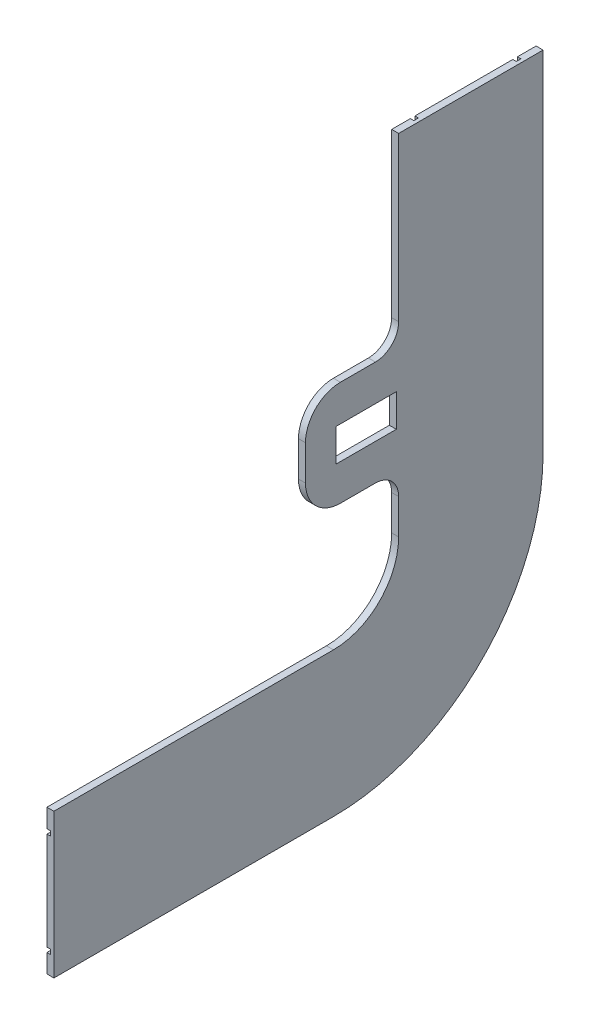
SolidWorks part; units mm, degrees
ref_plane "Front Plane" through (0, 0, 0) normal (0, 0, 1) x (1, 0, 0)
ref_plane "Top Plane" through (0, 0, 0) normal (0, 1, 0) x (1, 0, 0)
ref_plane "Right Plane" through (0, 0, 0) normal (1, 0, 0) x (0, 0, -1)
sketch "Sketch1" plane through (0, 0, 0) normal (1, 0, 0) x (0, 0, -1)
  line L0 (90, 0) -> (0, 0) construction
  line L1 (0, 0) -> (0, -90) construction
  line L2 (0, -28) -> (-120, -28)
  line L3 (-120, -28) -> (-120, -90)
  line L4 (-120, -90) -> (0, -90)
  line L5 (28, 0) -> (28, 150)
  line L6 (28, 150) -> (90, 150)
  line L7 (90, 150) -> (90, 0)
  arc A0 (0, -90) -> (90, 0) centre (0, 0) ccw
  arc A1 (0, -28) -> (28, 0) centre (0, 0) ccw
  dimension "D1" = 180
  dimension "D2" = 62
  dimension "D3" = 120
  dimension "D4" = 150
extrude "Boss-Extrude1" add sketch "Sketch1" along normal blind 3
sketch "Sketch2" plane through (3, 0, 0) normal (1, 0, 0) x (0, 0, -1)
  line L0 (0, 0) -> (90, 0) construction
  line L1 (0, 0) -> (0, -90) construction
  line L2 (0, -38) -> (-120, -38)
  line L3 (-120, -28) -> (-120, -90) construction
  line L4 (0, -80) -> (-120, -80)
  line L5 (38, 0) -> (38, 150)
  line L6 (90, 150) -> (28, 150) construction
  line L7 (80, 0) -> (80, 150)
  line L8 (36, 0) -> (36, 150)
  line L9 (0, -36) -> (-120, -36)
  line L10 (0, -82) -> (-120, -82)
  line L11 (82, 0) -> (82, 150)
  line L12 (36, 150) -> (38, 150)
  line L13 (80, 150) -> (82, 150)
  line L14 (-120, -80) -> (-120, -82)
  line L15 (-120, -36) -> (-120, -38)
  arc A0 (0, -38) -> (38, 0) centre (0, 0) ccw
  arc A1 (0, -80) -> (80, 0) centre (0, 0) ccw
  arc A2 (0, -36) -> (36, 0) centre (0, 0) ccw
  arc A3 (0, -82) -> (82, 0) centre (0, 0) ccw
  dimension "D1" = 42
  dimension "D2" = 80
  dimension "D3" = 2
  dimension "D4" = 2
extrude "Cut-Extrude1" cut sketch "Sketch2" against normal blind 1.5
mirror "Mirror1" about plane through (3, 0, 0) normal (1, 0, 0) of bodies 102
delete or keep bodies "Body-Delete1" type delete bodies bodies 102
sketch "Sketch5" plane through (6, 0, 0) normal (1, 0, 0) x (0, 0, -1)
  line L0 (28, 150) -> (28, 0) construction
  line L1 (28, 25) -> (-12, 25)
  line L2 (28, 25) -> (28, 70)
  line L3 (28, 70) -> (-12, 70)
  line L4 (-12, 25) -> (-12, 70)
  dimension "D1" = 40
  dimension "D2" = 45
  dimension "D3" = 25
extrude "Boss-Extrude2" add sketch "Sketch5" against normal blind 3 separate body
sketch "Sketch6" plane through (6, 0, 0) normal (1, 0, 0) x (0, 0, -1)
  line L0 (28, 47.5) -> (-12, 47.5) construction
  line L1 (28, 25) -> (28, 70) construction
  line L2 (-12, 70) -> (-12, 25) construction
  line L3 (28, 150) -> (28, 0) construction
  line L4 (1, 40.5) -> (27, 40.5)
  line L5 (1, 40.5) -> (1, 54.5)
  line L6 (1, 54.5) -> (27, 54.5)
  line L7 (27, 40.5) -> (27, 54.5)
  line L8 (1, 40.5) -> (27, 54.5) construction
  line L9 (1, 54.5) -> (27, 40.5) construction
  point P6 (14, 47.5)
  dimension "D1" = 1
  dimension "D2" = 26
  dimension "D3" = 14
extrude "Cut-Extrude2" cut sketch "Sketch6" against normal blind 3
sketch "Sketch7" plane through (6, 0, 0) normal (1, 0, 0) x (0, 0, -1)
  line L0 (28, 70) -> (-12, 70) construction
  line L1 (21.2489, 70) -> (31.6871, 70)
  line L2 (21.2489, 70) -> (21.2489, 54.5)
  line L3 (21.2489, 54.5) -> (31.6871, 54.5)
  line L4 (31.6871, 70) -> (31.6871, 54.5)
  line L6 (-12, 25) -> (28, 25) construction
  line L7 (19.2866, 25) -> (37.5074, 25)
  line L8 (19.2866, 25) -> (19.2866, 40.5)
  line L9 (19.2866, 40.5) -> (37.5074, 40.5)
  line L10 (37.5074, 25) -> (37.5074, 40.5)
  dimension "D1" = 15.5
  dimension "D2" = 15.5
fillet "Fillet1" radius 15 2 edges at (4.5, 70, 12) (4.5, 25, 12)
sketch "Sketch8" plane through (6, 0, 0) normal (1, 0, 0) x (0, 0, -1)
  line L0 (-120, -90) -> (0, -90) construction
  line L2 (-30, -100) -> (0, -100)
  line L3 (-30, -100) -> (-30, -90)
  line L4 (-30, -90) -> (0, -90)
  line L5 (0, -100) -> (0, -90)
  circle A0 centre (-15, -100) radius 15
  dimension "D1" = 30
  dimension "D2" = 10
  dimension "D3" = 15
sketch "Sketch9" plane through (6, 0, 0) normal (1, 0, 0) x (0, 0, -1)
  circle A0 centre (-15, -100) radius 2.7
  dimension "D1" = 5.4
extrude "Boss-Extrude3" add sketch "Sketch7" against normal blind 3
fillet "Fillet2" radius 10 2 edges at (4.5, 70, -28) (4.5, 25, -28)
